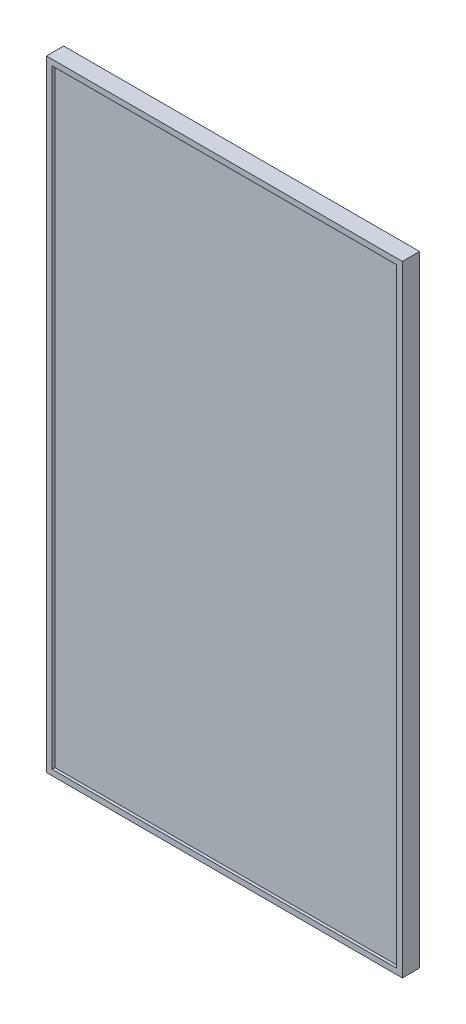
SolidWorks part; units mm, degrees
ref_plane "Front Plane" through (0, 0, 0) normal (0, 0, 1) x (1, 0, 0)
ref_plane "Top Plane" through (0, 0, 0) normal (0, 1, 0) x (1, 0, 0)
ref_plane "Right Plane" through (0, 0, 0) normal (1, 0, 0) x (0, 0, -1)
sketch "Sketch1" plane through (0, 0, 0) normal (0, 0, 1) x (1, 0, 0)
  line L1 (-314.55, -548.45) -> (314.55, -548.45)
  line L2 (-314.55, -548.45) -> (-314.55, 548.45)
  line L3 (-314.55, 548.45) -> (314.55, 548.45)
  line L4 (314.55, -548.45) -> (314.55, 548.45)
  line L5 (-314.55, -548.45) -> (314.55, 548.45) construction
  line L6 (-314.55, 548.45) -> (314.55, -548.45) construction
  point P0 (0, 0)
  dimension "D1" = 1096.9
  dimension "D2" = 629.1
extrude "Boss-Extrude1" add sketch "Sketch1" along normal blind 30.5
sketch "Sketch2" plane through (0, 0, 0) normal (0, 0, -1) x (-1, 0, 0)
  line L1 (-200, -200) -> (200, -200) construction
  line L2 (-200, -200) -> (-200, 200) construction
  line L3 (-200, 200) -> (200, 200) construction
  line L4 (200, -200) -> (200, 200) construction
  line L5 (-200, -200) -> (200, 200) construction
  line L6 (-200, 200) -> (200, -200) construction
  circle A0 centre (-200, 200) radius 4
  circle A1 centre (200, 200) radius 4
  circle A2 centre (200, -200) radius 4
  circle A3 centre (-200, -200) radius 4
  point P0 (0, 0)
  dimension "D3" = 8
  dimension "D1" = 400
  dimension "D2" = 400
extrude "Cut-Extrude1" cut sketch "Sketch2" against normal blind 21
sketch "Sketch3" plane through (0, 0, 30.5) normal (0, 0, 1) x (1, 0, 0)
  line L0 (314.55, 548.45) -> (-314.55, 548.45) construction
  line L1 (304.55, -538.45) -> (-304.55, -538.45)
  line L2 (304.55, -538.45) -> (304.55, 538.45)
  line L3 (304.55, 538.45) -> (-304.55, 538.45)
  line L4 (-304.55, -538.45) -> (-304.55, 538.45)
  line L5 (304.55, -538.45) -> (-304.55, 538.45) construction
  line L6 (304.55, 538.45) -> (-304.55, -538.45) construction
  line L7 (-314.55, 548.45) -> (-314.55, -548.45) construction
  point P0 (0, 0)
  dimension "D1" = 10
  dimension "D2" = 10
extrude "Cut-Extrude2" cut sketch "Sketch3" against normal blind 5
